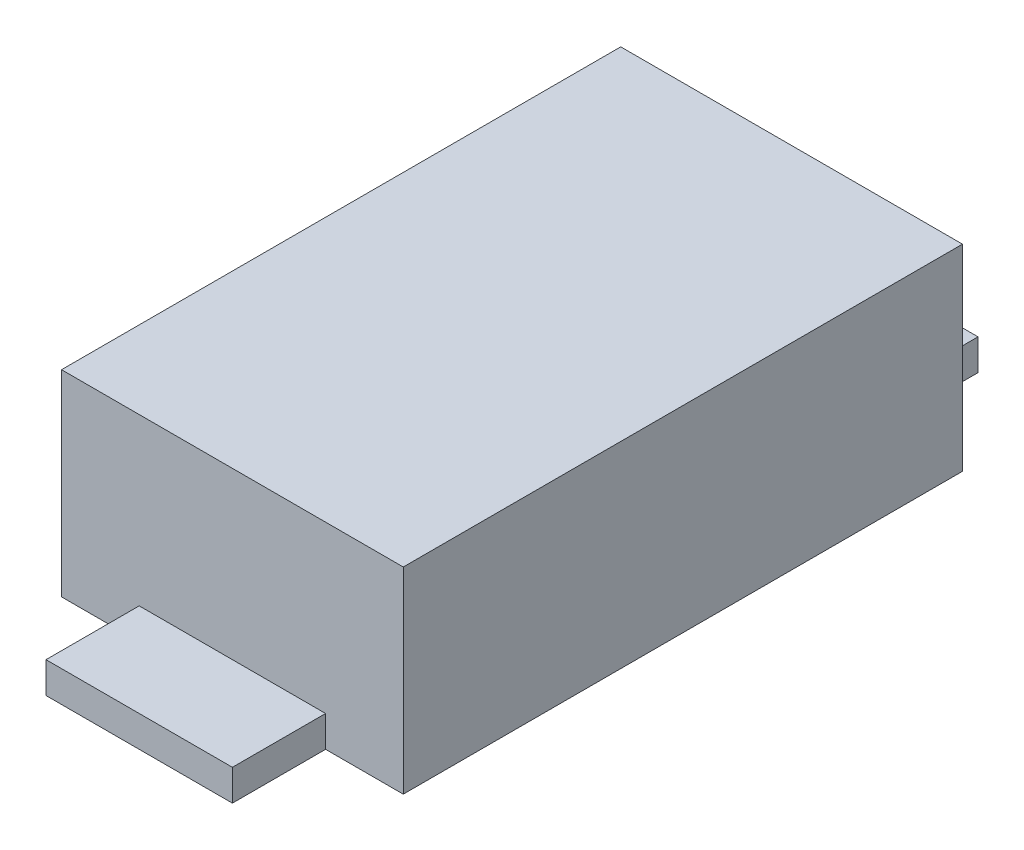
SolidWorks part; units mm, degrees
ref_plane "Front Plane" through (0, 0, 0) normal (0, 0, 1) x (1, 0, 0)
ref_plane "Top Plane" through (0, 0, 0) normal (0, 1, 0) x (1, 0, 0)
ref_plane "Right Plane" through (0, 0, 0) normal (1, 0, 0) x (0, 0, -1)
sketch "BaseS" plane through (0, 0, 0) normal (0, 1, 0) x (1, 0, 0)
  line L1 (-0.825, 1.35) -> (0.825, 1.35)
  line L2 (-0.825, 1.35) -> (-0.825, -1.35)
  line L3 (-0.825, -1.35) -> (0.825, -1.35)
  line L4 (0.825, 1.35) -> (0.825, -1.35)
  line L5 (-0.825, 1.35) -> (0.825, -1.35) construction
  line L6 (-0.825, -1.35) -> (0.825, 1.35) construction
  point P0 (0, 0)
  dimension "Width" = 1.65
  dimension "Length" = 2.7
extrude "Base" add sketch "BaseS" along normal blind 0.95
sketch "LegS" plane through (0, 0, 0) normal (0, 1, 0) x (1, 0, 0)
  line L0 (0.825, 1.35) -> (-0.825, 1.35) construction
  line L1 (-0.45, 1.35) -> (0.45, 1.35)
  line L2 (-0.45, 1.35) -> (-0.45, 1.8)
  line L3 (-0.45, 1.8) -> (0.45, 1.8)
  line L4 (0.45, 1.35) -> (0.45, 1.8)
  point P6 (0, 1.35)
  dimension "Length" = 0.45
  dimension "Width" = 0.9
extrude "Leg" add sketch "LegS" along normal blind 0.15
mirror "LVM" about plane through (0, 0, 0) normal (0, 0, 1) of "Leg"
